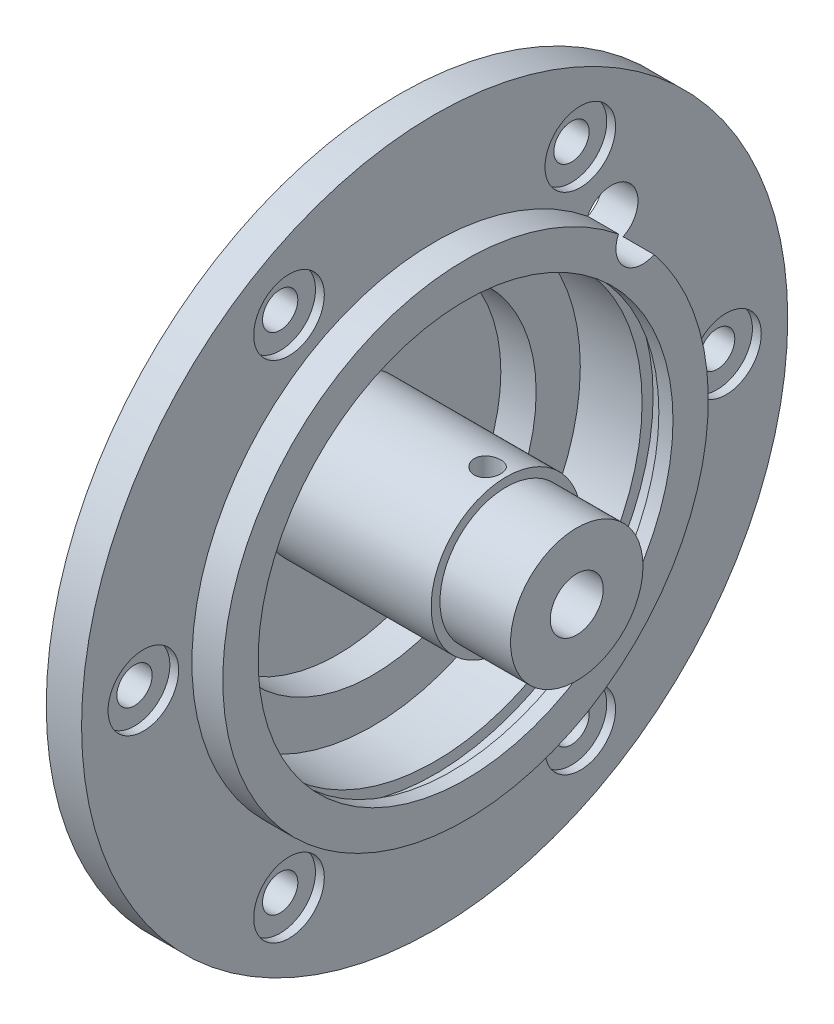
SolidWorks part; units mm, degrees
ref_plane "Front Plane" through (0, 0, 0) normal (0, 0, 1) x (1, 0, 0)
ref_plane "Top Plane" through (0, 0, 0) normal (0, 1, 0) x (1, 0, 0)
ref_plane "Right Plane" through (0, 0, 0) normal (1, 0, 0) x (0, 0, -1)
sketch "Sketch1" plane through (0, 0, 0) normal (1, 0, 0) x (0, 0, -1)
  circle A0 centre (0, 0) radius 40
extrude "Boss-Extrude1" add sketch "Sketch1" along normal blind 27
sketch "Sketch2" plane through (0, 0, 0) normal (-1, 0, 0) x (0, 0, 1)
  circle A0 centre (0, 0) radius 3
extrude "Cut-Extrude1" cut sketch "Sketch2" against normal blind 45 and the other way through all
sketch "Sketch3" plane through (27, 0, 0) normal (1, 0, 0) x (0, 0, -1)
  circle A0 centre (0, 0) radius 8.5
  circle A1 centre (0, 0) radius 18.5
extrude "Cut-Extrude2" cut sketch "Sketch3" against normal blind 23
sketch "Sketch4" plane through (27, 0, 0) normal (1, 0, 0) x (0, 0, -1)
  circle A0 centre (0, 0) radius 23.5
  circle A1 centre (0, 0) radius 18.5
extrude "Cut-Extrude5" cut sketch "Sketch4" against normal blind 19
sketch "Sketch6" plane through (0, 0, 0) normal (-1, 0, 0) x (0, 0, 1)
  circle A0 centre (0, 0) radius 22.5
  circle A1 centre (0, 0) radius 40
extrude "Cut-Extrude6" cut sketch "Sketch6" against normal blind 4
sketch "Sketch7" plane through (27, 0, 0) normal (1, 0, 0) x (0, 0, -1)
  circle A0 centre (0, 0) radius 40
  circle A1 centre (0, 0) radius 27.5
extrude "Cut-Extrude7" cut sketch "Sketch7" against normal blind 12
sketch "Sketch8" plane through (27, 0, 0) normal (1, 0, 0) x (0, 0, -1)
  circle A0 centre (0, 0) radius 35
  circle A1 centre (0, 0) radius 8.5
extrude "Cut-Extrude8" cut sketch "Sketch8" against normal blind 8.5
ref_plane "Plane5" through (15.95, 0, 0) normal (1, 0, 0) x (0, 0, -1)
sketch "Sketch9" plane through (15.95, 0, 0) normal (1, 0, 0) x (0, 0, -1)
  circle A0 centre (0, 0) radius 24.75
  circle A1 centre (0, 0) radius 8.5
extrude "Cut-Extrude13" cut sketch "Sketch9" against normal mid plane 1.9
sketch "Sketch10" plane through (15, 0, 0) normal (1, 0, 0) x (0, 0, -1)
  line L0 (0, 0) -> (40, 0) construction
  line L1 (0, 0) -> (20.0323, 20.0323) construction
  circle A0 centre (20.0323, 20.0323) radius 3
  circle A1 centre (0, 0) radius 40 construction
  dimension "D1" = 28.33
  dimension "D3" = 6
  dimension "D2" = 45
extrude "Cut-Extrude14" cut sketch "Sketch10" against normal through all both and the other way through all
sketch "Sketch11" plane through (15, 0, 0) normal (1, 0, 0) x (0, 0, -1)
  circle A0 centre (33, 0) radius 2
  dimension "D1" = 33
extrude "Cut-Extrude22" cut sketch "Sketch11" against normal up to next (11 mm away)
sketch "Sketch12" plane through (15, 0, 0) normal (1, 0, 0) x (0, 0, -1)
  circle A0 centre (33, 0) radius 4
extrude "Cut-Extrude23" cut sketch "Sketch12" against normal blind 1
pattern_circular "CirPattern1" count 6 over 360 about axis through (0, 0, 0) along (1, 0, 0) of "Cut-Extrude23", "Cut-Extrude22"
sketch "Sketch13" plane through (0, 0, 0) normal (0, 1, 0) x (1, 0, 0)
  circle A1 centre (21, 0) radius 1.5
  dimension "D1" = 21
extrude "Cut-Extrude24" cut sketch "Sketch13" along normal up to next
sketch "Sketch14" plane through (4, 0, 0) normal (-1, 0, 0) x (0, 0, 1)
  circle A0 centre (0, 0) radius 27
  circle A1 centre (0, 0) radius 40
extrude "Cut-Extrude25" cut sketch "Sketch14" against normal blind 7
sketch "Sketch15" plane through (0, 0, 0) normal (0, 0, 1) x (1, 0, 0)
  circle A0 centre (21, 0) radius 1.5
  dimension "D1" = 21
extrude "Cut-Extrude26" cut sketch "Sketch15" against normal up to next
sketch "Sketch16" plane through (27, 0, 0) normal (1, 0, 0) x (0, 0, -1)
  circle A0 centre (0, 0) radius 8.5
extrude "Boss-Extrude2" add sketch "Sketch16" along normal blind 4.1
sketch "Sketch17" plane through (31.1, 0, 0) normal (1, 0, 0) x (0, 0, -1)
  circle A0 centre (0, 0) radius 7.5
  circle A1 centre (0, 0) radius 8.5
extrude "Cut-Extrude27" cut sketch "Sketch17" against normal blind 8
sketch "Sketch18" plane through (31.1, 0, 0) normal (1, 0, 0) x (0, 0, -1)
  circle A0 centre (0, 0) radius 3
extrude "Cut-Extrude28" cut sketch "Sketch18" against normal blind 7
